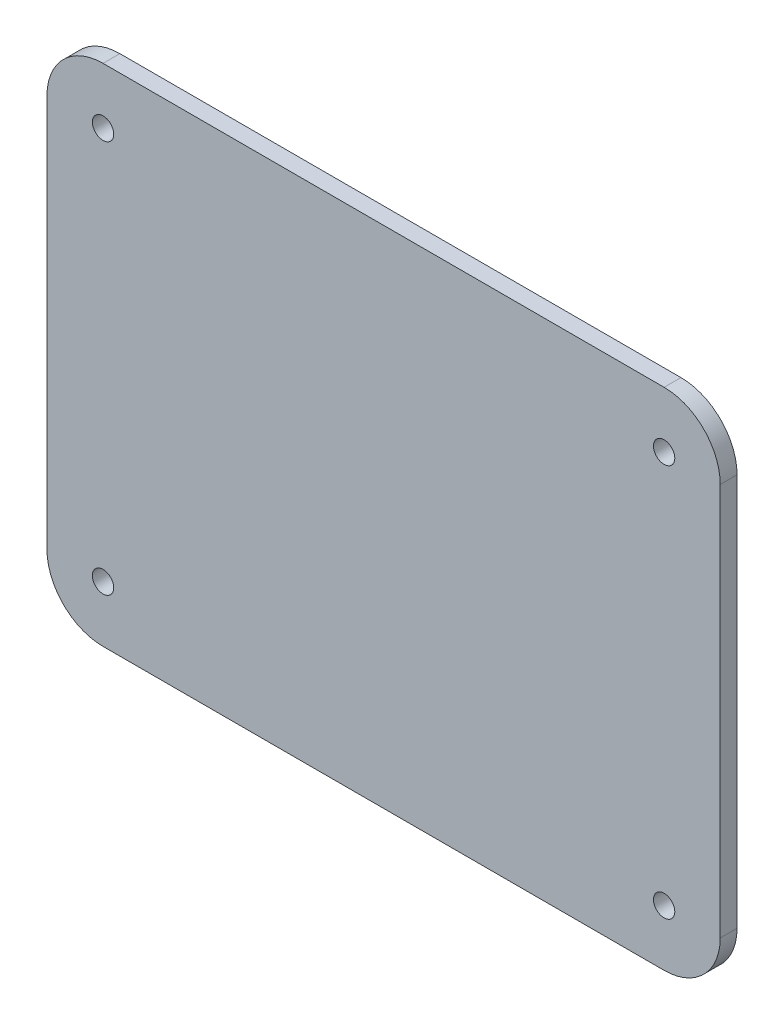
SolidWorks part; units mm, degrees
ref_plane "Front Plane" through (0, 0, 0) normal (0, 0, 1) x (1, 0, 0)
ref_plane "Top Plane" through (0, 0, 0) normal (0, 1, 0) x (1, 0, 0)
ref_plane "Right Plane" through (0, 0, 0) normal (1, 0, 0) x (0, 0, -1)
sketch "Sketch3" plane through (0, 0, 0) normal (0, 0, 1) x (1, 0, 0)
  line L1 (-50, 45) -> (50, 45)
  line L2 (-60, 35) -> (-60, -35)
  line L3 (-50, -45) -> (50, -45)
  line L4 (60, 35) -> (60, -35)
  line L5 (-60, 45) -> (60, -45) construction
  line L6 (-60, -45) -> (60, 45) construction
  arc A0 (-60, -35) -> (-50, -45) centre (-50, -35) ccw
  arc A1 (50, -45) -> (60, -35) centre (50, -35) ccw
  arc A2 (60, 35) -> (50, 45) centre (50, 35) ccw
  arc A3 (-50, 45) -> (-60, 35) centre (-50, 35) ccw
  circle A4 centre (-50, 35) radius 1.9
  circle A5 centre (50, 35) radius 1.9
  circle A6 centre (50, -35) radius 1.9
  circle A7 centre (-50, -35) radius 1.9
  point P0 (0, 0)
  dimension "D3" = 10
  dimension "D1" = 120
  dimension "D2" = 90
extrude "Boss-Extrude2" add sketch "Sketch3" along normal blind 3
